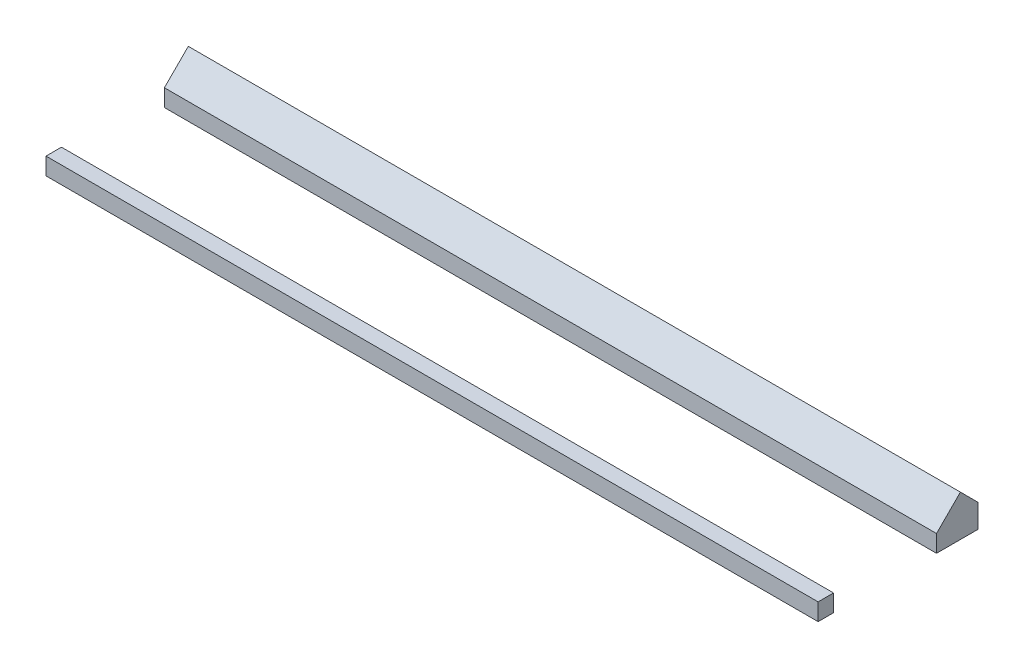
SolidWorks part; units mm, degrees
material "FG260"
ref_plane "Front Plane" through (0, 0, 0) normal (0, 0, 1) x (1, 0, 0)
ref_plane "Top Plane" through (0, 0, 0) normal (0, 1, 0) x (1, 0, 0)
ref_plane "Right Plane" through (0, 0, 0) normal (1, 0, 0) x (0, 0, -1)
sketch "Sketch2" plane through (0, 0, 0) normal (1, 0, 0) x (0, 0, -1)
  line L9 (-60, 20) -> (-78, 20)
  line L10 (-78, 20) -> (-78, 0)
  line L15 (-78, 0) -> (-60, 0)
  line L16 (87.86, 47.86) -> (60, 20)
  line L19 (60, 22.5753) -> (60, 17.1372) construction
  line L20 (87.86, 47.86) -> (108.3661, 27.3539)
  line L21 (108.3661, 27.3539) -> (108.3661, 0)
  line L22 (60, 0) -> (108.3661, 0)
  line L23 (-60, 20) -> (-60, 0)
  line L24 (60, 20) -> (60, 0)
  dimension "D1" = 20
  dimension "D2" = 60
  dimension "D3" = 18
  dimension "D4" = 60
  dimension "D10" = 39.4
  dimension "D11" = 45
  dimension "D12" = 29
extrude "Boss-Extrude1" add sketch "Sketch2" along normal blind 900
